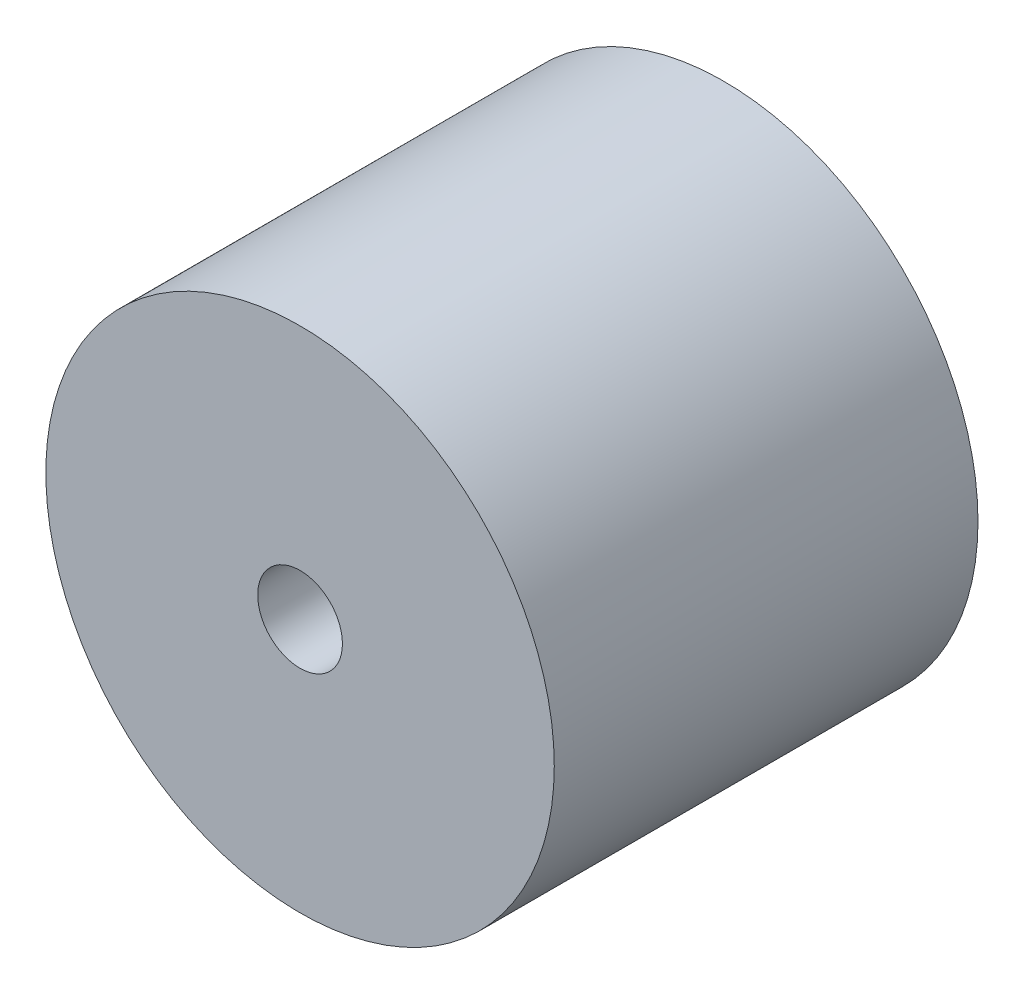
SolidWorks part; units mm, degrees
ref_plane "Front Plane" through (0, 0, 0) normal (0, 0, 1) x (1, 0, 0)
ref_plane "Top Plane" through (0, 0, 0) normal (0, 1, 0) x (1, 0, 0)
ref_plane "Right Plane" through (0, 0, 0) normal (1, 0, 0) x (0, 0, -1)
sketch "Sketch1" plane through (0, 0, 0) normal (0, 0, 1) x (1, 0, 0)
  circle A0 centre (0, 0) radius 3
  circle A1 centre (0, 0) radius 18
  dimension "D1" = 36
  dimension "D2" = 6
extrude "Boss-Extrude1" add sketch "Sketch1" along normal mid plane 30
